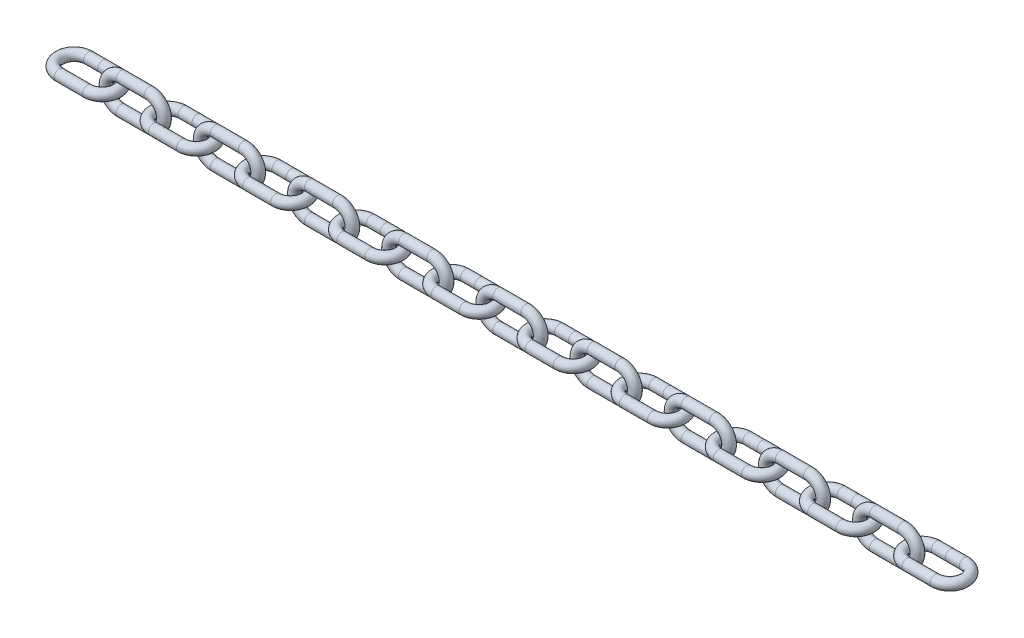
SolidWorks part; units mm, degrees
material "Plain Carbon Steel"
ref_plane "Front Plane" through (0, 0, 0) normal (0, 0, 1) x (1, 0, 0)
ref_plane "Top Plane" through (0, 0, 0) normal (0, 1, 0) x (1, 0, 0)
ref_plane "Right Plane" through (0, 0, 0) normal (1, 0, 0) x (0, 0, -1)
sketch "Sketch1" plane through (0, 0, 0) normal (0, 1, 0) x (1, 0, 0)
  line L0 (9.398, 9.8425) -> (-9.398, 9.8425)
  line L1 (-9.398, -9.8425) -> (9.398, -9.8425)
  line L2 (9.398, 0) -> (-9.398, 0) construction
  line L3 (9.398, 6.35) -> (-9.398, 6.35) construction
  line L4 (-9.398, -6.35) -> (9.398, -6.35) construction
  arc A0 (-9.398, 9.8425) -> (-9.398, -9.8425) centre (-9.398, 0) ccw
  arc A1 (9.398, -9.8425) -> (9.398, 9.8425) centre (9.398, 0) ccw
  arc A2 (9.398, -6.35) -> (9.398, 6.35) centre (9.398, 0) ccw construction
  arc A3 (-9.398, 6.35) -> (-9.398, -6.35) centre (-9.398, 0) ccw construction
  point P13 (-15.748, 0)
  point P14 (15.748, 0)
  dimension "D1" = 31.496
  dimension "D4" = 12.7
  dimension "D3" = 3.4925
sketch "Sketch2" plane through (0, 0, 0) normal (1, 0, 0) x (0, 0, -1)
  circle A0 centre (9.8425, 0) radius 3.4925
  dimension "D1" = 6.985
sweep "Sweep1" add profiles "Sketch2" path "Sketch1"
sketch "Sketch5" plane through (0, 0, 0) normal (0, 0, 1) x (1, 0, 0)
  line L0 (-22.098, 9.8425) -> (-40.894, 9.8425)
  line L1 (-40.894, -9.8425) -> (-22.098, -9.8425)
  line L2 (-22.098, 6.35) -> (-40.894, 6.35) construction
  line L3 (-40.894, -6.35) -> (-22.098, -6.35) construction
  arc A0 (-40.894, 9.8425) -> (-40.894, -9.8425) centre (-40.894, 0) ccw
  arc A1 (-22.098, -9.8425) -> (-22.098, 9.8425) centre (-22.098, 0) ccw
  circle A2 centre (-19.2405, 0) radius 3.4925
  arc A3 (-22.098, -6.35) -> (-22.098, 6.35) centre (-22.098, 0) ccw construction
  arc A4 (-40.894, 6.35) -> (-40.894, -6.35) centre (-40.894, 0) ccw construction
  arc A5 (-40.894, 9.8425) -> (-40.894, -9.8425) centre (-40.894, 0) ccw construction
  point P5 (-47.244, 0)
  point P6 (-19.2405, 0)
  point P20 (-15.748, 0)
  dimension "D3" = 6.985
  dimension "D1" = 31.496
  dimension "D2" = 12.7
  dimension "D5" = 3.4925
ref_plane "Plane1" through (-22.098, 9.8425, 0) normal (-1, 0, 0) x (0, 0, 1)
sketch "Sketch6" plane through (-22.098, 9.8425, 0) normal (-1, 0, 0) x (0, 0, 1)
  circle A0 centre (0, 0) radius 3.4925
  dimension "D1" = 6.985
sweep "Sweep2" add profiles "Sketch6" path "Sketch5"
pattern_linear "LPattern1" count 9 spacing 62.992 along (1, 0, 0) of bodies 102 101
sketch "Sketch7" [suppressed] plane through (0, 0, 0) normal (0, 0, 1) x (1, 0, 0)
  line L0 (-54.61, 0) -> (2702.9811, 0)
  arc A0 (-41.275, 13.335) -> (-41.275, -13.335) centre (-41.275, 0) ccw construction
  dimension "D1" = 2757.5911
pattern_linear "LPattern3" count 2 spacing 62.992 along (-1, 0, 0) of bodies 101
